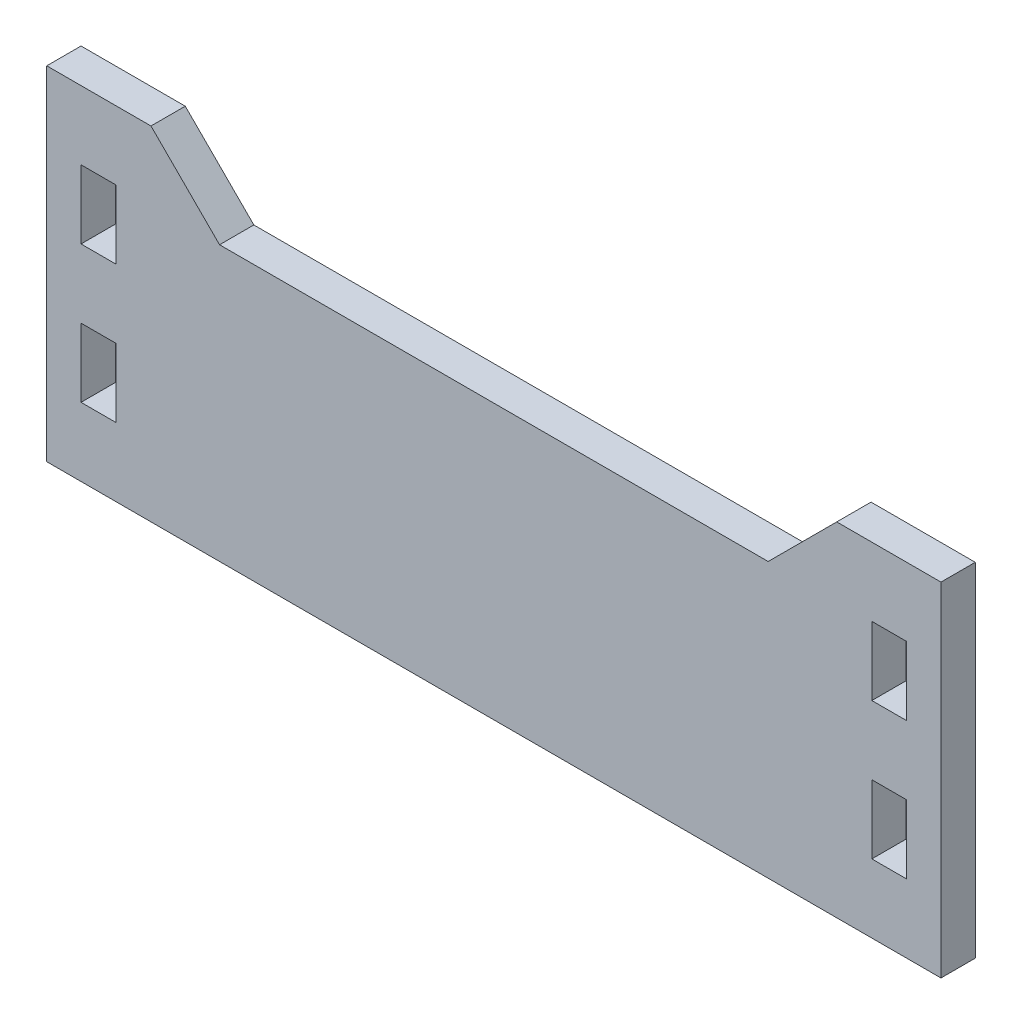
SolidWorks part; units mm, degrees
ref_plane "Front Plane" through (0, 0, 0) normal (0, 0, 1) x (1, 0, 0)
ref_plane "Top Plane" through (0, 0, 0) normal (0, 1, 0) x (1, 0, 0)
ref_plane "Right Plane" through (0, 0, 0) normal (1, 0, 0) x (0, 0, -1)
sketch "Sketch1" plane through (0, 0, 0) normal (0, 0, 1) x (1, 0, 0)
  line L1 (-41.402, -15.875) -> (41.402, -15.875)
  line L2 (-41.402, -15.875) -> (-41.402, 15.875)
  line L3 (-41.402, 15.875) -> (41.402, 15.875)
  line L4 (41.402, -15.875) -> (41.402, 15.875)
  line L5 (-41.402, -15.875) -> (41.402, 15.875) construction
  line L6 (-41.402, 15.875) -> (41.402, -15.875) construction
  point P0 (0, 0)
  dimension "D1" = 82.804
  dimension "D2" = 31.75
extrude "Boss-Extrude1" add sketch "Sketch1" along normal blind 3.175
sketch "Sketch2" plane through (0, 0, 3.175) normal (0, 0, 1) x (1, 0, 0)
  line L0 (-41.402, 15.875) -> (-41.402, -15.875) construction
  line L1 (-38.227, 9.525) -> (-35.0012, 9.525)
  line L2 (-38.227, 9.525) -> (-38.227, 3.175)
  line L3 (-38.227, 3.175) -> (-35.0012, 3.175)
  line L4 (-35.0012, 9.525) -> (-35.0012, 3.175)
  line L5 (-38.227, 9.525) -> (-35.0012, 3.175) construction
  line L6 (-38.227, 3.175) -> (-35.0012, 9.525) construction
  line L7 (-38.227, -3.175) -> (-35.0012, -3.175)
  line L8 (-38.227, -3.175) -> (-38.227, -9.525)
  line L9 (-38.227, -9.525) -> (-35.0012, -9.525)
  line L10 (-35.0012, -3.175) -> (-35.0012, -9.525)
  line L11 (-38.227, -3.175) -> (-35.0012, -9.525) construction
  line L12 (-38.227, -9.525) -> (-35.0012, -3.175) construction
  line L13 (-41.402, 0) -> (0, 0) construction
  point P0 (-36.6141, 6.35)
  point P5 (-36.6141, -6.35)
  dimension "D1" = 3.175
  dimension "D2" = 3.2258
  dimension "D3" = 6.35
  dimension "D4" = 3.2258
  dimension "D5" = 6.35
  dimension "D6" = 3.175
  dimension "D7" = 3.175
  dimension "D8" = 3.175
extrude "cut for tab" cut sketch "Sketch2" against normal through all
mirror "Mirror1" about plane through (0, 0, 0) normal (1, 0, 0) of "cut for tab"
sketch "Sketch3" plane through (0, 0, 3.175) normal (0, 0, 1) x (1, 0, 0)
  line L0 (0, 15.875) -> (0, 9.525)
  line L1 (41.402, 15.875) -> (-41.402, 15.875) construction
  line L2 (0, 9.525) -> (-25.4, 9.525)
  line L3 (-25.4, 9.525) -> (-31.75, 15.875)
  line L4 (-31.75, 15.875) -> (0, 15.875)
  dimension "D1" = 45
  dimension "D2" = 6.35
  dimension "D3" = 31.75
extrude "Cut-Extrude1" cut sketch "Sketch3" against normal through all
mirror "Mirror2" about plane through (0, 0, 0) normal (1, 0, 0) of "Cut-Extrude1"
